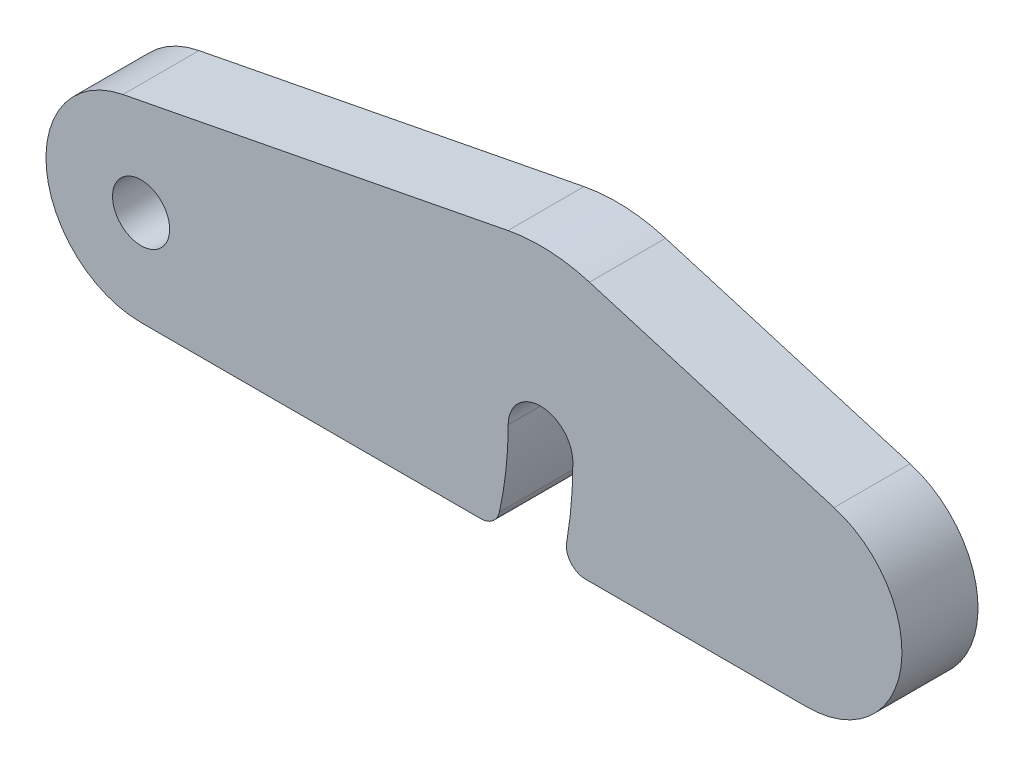
SolidWorks part; units mm, degrees
ref_plane "Front Plane" through (0, 0, 0) normal (0, 0, 1) x (1, 0, 0)
ref_plane "Top Plane" through (0, 0, 0) normal (0, 1, 0) x (1, 0, 0)
ref_plane "Right Plane" through (0, 0, 0) normal (1, 0, 0) x (0, 0, -1)
sketch "Sketch1" plane through (0, 0, 0) normal (0, 0, 1) x (1, 0, 0)
  line L0 (-17.9762, 2.4542) -> (17.0238, 2.4542) construction
  line L2 (-17.9762, -2.5458) -> (17.0238, -2.5458)
  line L3 (-18.9286, 7.3627) -> (1.3095, 11.2895)
  line L4 (18.4524, 7.2458) -> (5.5952, 11.0791)
  arc A0 (-18.9286, 7.3627) -> (-17.9762, -2.5458) centre (-17.9762, 2.4542) ccw
  arc A1 (17.0238, -2.5458) -> (18.4524, 7.2458) centre (17.0238, 2.4542) ccw
  circle A2 centre (-17.9762, 2.4542) radius 1.5
  circle A3 centre (3.0238, 2.4542) radius 1.7
  arc A5 (5.5952, 11.0791) -> (1.3095, 11.2895) centre (3.0238, 2.4542) ccw
  point P2 (0, 0)
  dimension "D2" = 3
  dimension "D3" = 3.4
  dimension "D1" = 5
  dimension "D4" = 21
  dimension "D5" = 35
extrude "Boss-Extrude1" add sketch "Sketch1" along normal blind 4
sketch "Sketch2" plane through (0, 0, 4) normal (0, 0, 1) x (1, 0, 0)
  line L0 (-1.8352, -8.1268) -> (2.1069, -8.1268)
  arc A0 (-1.8352, -8.1268) -> (1.3238, 2.4542) centre (-17.9762, 2.4542) ccw
  arc A1 (2.1069, -8.1268) -> (4.7238, 2.4542) centre (-17.9762, 2.4542) ccw
  arc A2 (4.7238, 2.4542) -> (1.3238, 2.4542) centre (3.0238, 2.4542) ccw
  circle A3 centre (3.0238, 2.4542) radius 1.7 construction
extrude "Cut-Extrude1" cut sketch "Sketch2" against normal through all
fillet "Fillet1" radius 1 2 edges at (4.1663, -2.5458, 2) (0.6649, -2.5458, 2)
